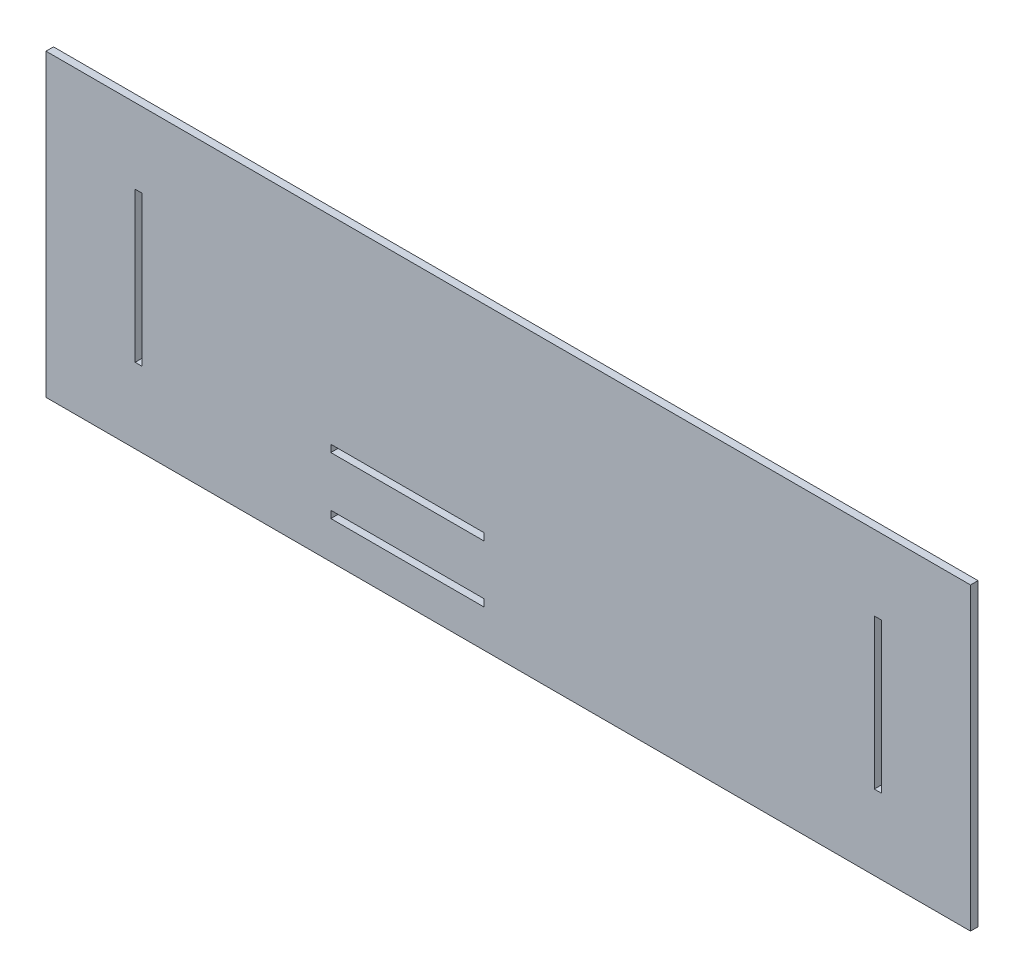
SolidWorks part; units mm, degrees
ref_plane "Front Plane" through (0, 0, 0) normal (0, 0, 1) x (1, 0, 0)
ref_plane "Top Plane" through (0, 0, 0) normal (0, 1, 0) x (1, 0, 0)
ref_plane "Right Plane" through (0, 0, 0) normal (1, 0, 0) x (0, 0, -1)
sketch "Sketch2" plane through (0, 0, 0) normal (0, 0, 1) x (1, 0, 0)
  line L0 (0, 99.4467) -> (0, -105.6358) construction
  line L1 (-185, 60) -> (185, 60)
  line L2 (-185, 60) -> (-185, -60)
  line L3 (-185, -60) -> (185, -60)
  line L4 (185, 60) -> (185, -60)
  line L5 (-185, 60) -> (185, -60) construction
  line L6 (-185, -60) -> (185, 60) construction
  line L7 (-149.34, 30) -> (-146.5, 30)
  line L8 (-149.34, 30) -> (-149.34, -30)
  line L9 (-149.34, -30) -> (-146.5, -30)
  line L10 (-146.5, 30) -> (-146.5, -30)
  line L11 (-146.5, 0) -> (146.5, 0) construction
  line L12 (149.34, -30) -> (146.5, -30)
  line L13 (149.34, 30) -> (149.34, -30)
  line L14 (146.5, 30) -> (146.5, -30)
  line L15 (149.34, 30) -> (146.5, 30)
  line L17 (-71, -42.12) -> (-9.75, -42.12)
  line L18 (-71, -42.12) -> (-71, -45)
  line L19 (-71, -45) -> (-9.75, -45)
  line L20 (-9.75, -42.12) -> (-9.75, -45)
  line L21 (-71, -19.24) -> (-9.75, -19.24)
  line L22 (-71, -19.24) -> (-71, -22.12)
  line L23 (-71, -22.12) -> (-9.75, -22.12)
  line L24 (-9.75, -19.24) -> (-9.75, -22.12)
  point P0 (0, 0)
  point P15 (0, 0)
  point P17 (-146.5, 0)
  point P25 (-9.75, -43.56)
  dimension "D1" = 370
  dimension "D2" = 120
  dimension "D3" = 2.84
  dimension "D4" = 60
  dimension "D5" = 293
  dimension "D6" = 2.88
  dimension "D7" = 61.25
  dimension "D8" = 15
  dimension "D9" = 9.75
  dimension "D10" = 20
extrude "Boss-Extrude1" add sketch "Sketch2" along normal blind 3
